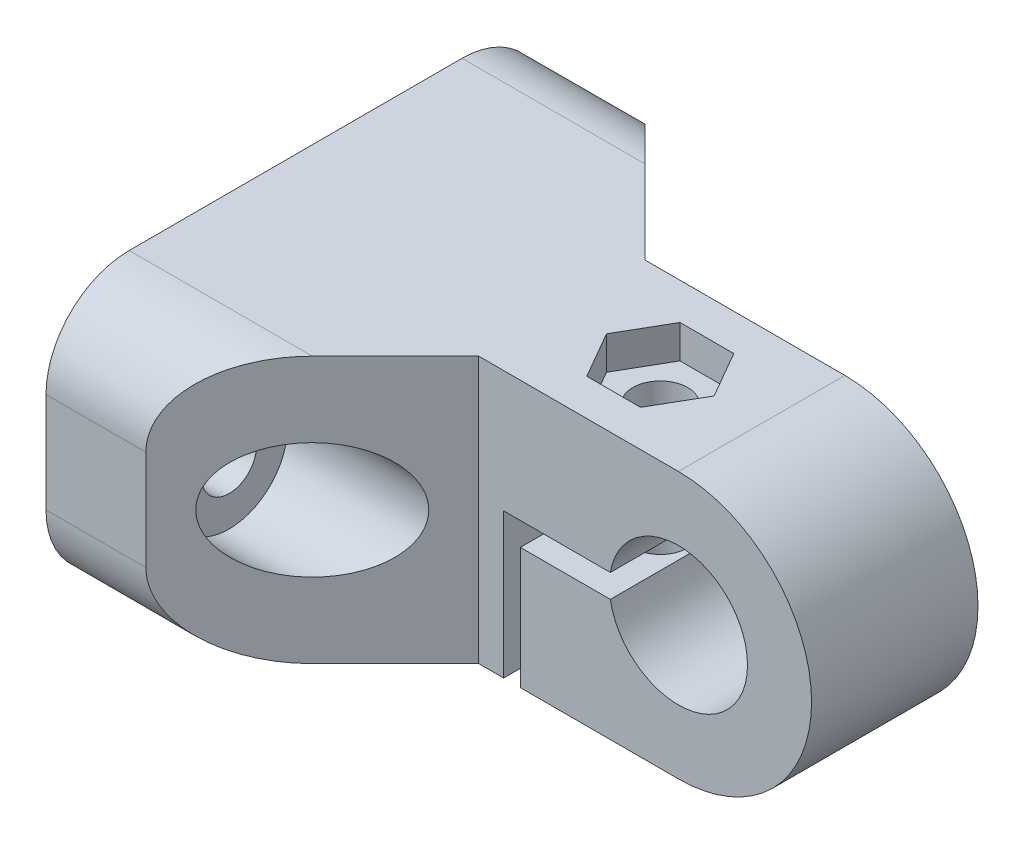
SolidWorks part; units mm, degrees
ref_plane "Plano frontal" through (0, 0, 0) normal (0, 0, 1) x (1, 0, 0)
ref_plane "Plano superior" through (0, 0, 0) normal (0, 1, 0) x (1, 0, 0)
ref_plane "Plano direito" through (0, 0, 0) normal (1, 0, 0) x (0, 0, -1)
sketch "Esboço2" plane through (0, 0, 0) normal (0, 0, 1) x (1, 0, 0)
  line L0 (0, 8) -> (-28, 8)
  line L1 (-28, 8) -> (-28, -8)
  line L2 (-28, -8) -> (-10.5, -8)
  line L3 (-4, 0) -> (-10, 0) construction
  line L4 (-10, 0) -> (-10, -8) construction
  line L5 (-4.0905, 0.7) -> (-10.5, 0.7)
  line L6 (-10.5, 0.7) -> (-10.5, -8)
  line L7 (-4.0905, -0.7) -> (-9.5, -0.7)
  line L8 (-9.5, -0.7) -> (-9.5, -8)
  line L11 (-9.5, -8) -> (0, -8)
  arc A0 (-4.0905, -0.7) -> (-4.0905, 0.7) centre (0, 0) ccw
  arc A1 (0, -8) -> (0, 8) centre (0, 0) ccw
  point P5 (-28, 0)
  dimension "D1" = 8.3
  dimension "D3" = 8
  dimension "D2" = 10
  dimension "D6" = 18
  dimension "D4" = 0.7
  dimension "D5" = 0.7
  dimension "D9" = 1
extrude "Ressalto-extrusão1" add sketch "Esboço2" along normal blind 30
sketch "Esboço8" plane through (0, 8, 0) normal (0, 1, 0) x (1, 0, 0)
  line L0 (-22, -30) -> (-12, -20)
  line L1 (-12, -20) -> (8, -20)
  line L2 (8, -30) -> (8, 0) construction
  line L3 (8, -20) -> (8, -30)
  line L4 (0, -30) -> (8, -30) construction
  line L5 (8, -30) -> (-22, -30)
  line L6 (-28, -15) -> (-21.8746, -15) construction
  line L7 (-28, -30) -> (-28, 0) construction
  line L8 (8, 0) -> (-22, 0)
  line L9 (8, -10) -> (8, 0)
  line L10 (-12, -10) -> (8, -10)
  line L11 (-22, 0) -> (-12, -10)
  dimension "D1" = 10
  dimension "D2" = 6
  dimension "D3" = 45
extrude "Corte-extrusão6" cut sketch "Esboço8" against normal through all
sketch "Esboço6" plane through (0, 0.7, 0) normal (0, -1, 0) x (1, 0, 0)
  line L0 (-4.0905, 20) -> (-4.0905, 10) construction
  line L2 (8, 10) -> (8, 20) construction
  circle A0 centre (-6.0905, 15) radius 1.65
  point P4 (7, 10)
  point P13 (8, 15)
  dimension "D1" = 3.3
  dimension "D2" = 2
extrude "Corte-extrusão4" cut sketch "Esboço6" against normal through all both and the other way through all
sketch "Esboço7" plane through (0, 8, 0) normal (0, 1, 0) x (1, 0, 0)
  line L1 (-2.8574, -15) -> (-4.474, -12.2)
  line L2 (-4.474, -12.2) -> (-7.7071, -12.2)
  line L3 (-7.7071, -12.2) -> (-9.3237, -15)
  line L4 (-9.3237, -15) -> (-7.7071, -17.8)
  line L5 (-7.7071, -17.8) -> (-4.474, -17.8)
  line L6 (-4.474, -17.8) -> (-2.8574, -15)
  circle A0 centre (-6.0905, -15) radius 2.8 construction
  dimension "D1" = 5.6
extrude "Corte-extrusão5" cut sketch "Esboço7" against normal blind 2
sketch "Esboço9" plane through (-28, 0, 19.4558) normal (1, 0, 0) x (0, 0, -1)
  line L0 (4.4558, 8) -> (4.4558, -3.4742) construction
  line L1 (-0.5442, 8) -> (9.4558, 8) construction
  line L2 (19.4558, 8) -> (9.4558, 8) construction
  circle A0 centre (14.4558, 0) radius 1.65
  circle A1 centre (-5.5442, 0) radius 1.65
  point P6 (0, 0)
  point P8 (14.4558, 8)
  point P13 (-5.5442, 8)
  dimension "D1" = 3.3
extrude "Corte-extrusão7" cut sketch "Esboço9" along normal through all
fillet "Filete1" radius 5 4 edges at (-25, -8, 0) (-25, 8, 0) (-25, -8, 30) (-25, 8, 30)
sketch "Esboço10" plane through (0, 0, 0) normal (1, 0, 0) x (0, 0, -1)
  circle A0 centre (-25, 0) radius 3.5
  circle A1 centre (-5, 0) radius 3.5
  dimension "D1" = 7
extrude "Corte-extrusão8" cut sketch "Esboço10" against normal offset from surface (22 mm away) 6 up to face at (-28, 0, 26.65)
